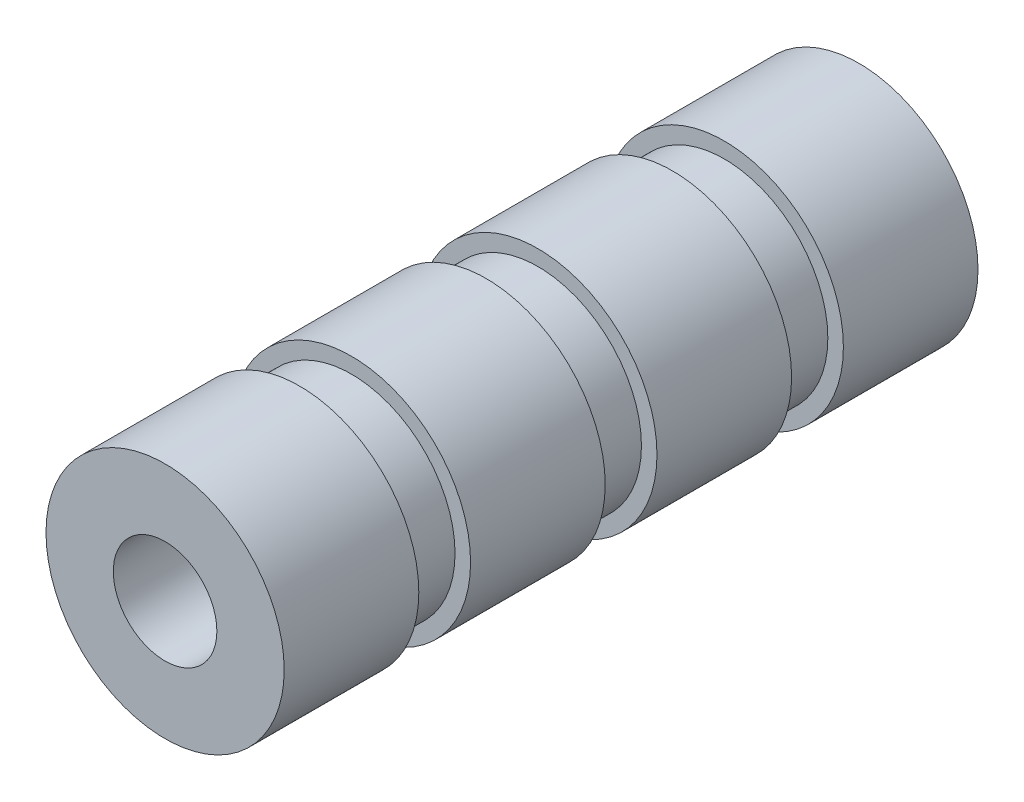
SolidWorks part; units mm, degrees
ref_plane "Front Plane" through (0, 0, 0) normal (0, 0, 1) x (1, 0, 0)
ref_plane "Top Plane" through (0, 0, 0) normal (0, 1, 0) x (1, 0, 0)
ref_plane "Right Plane" through (0, 0, 0) normal (1, 0, 0) x (0, 0, -1)
sketch "Sketch1" plane through (0, 0, 0) normal (0, 0, 1) x (1, 0, 0)
  circle A0 centre (0, 0) radius 11.5
  dimension "D1" = 23
extrude "Boss-Extrude1" add sketch "Sketch1" along normal blind 13
sketch "Sketch2" plane through (0, 0, 13) normal (0, 0, 1) x (1, 0, 0)
  circle A0 centre (0, 0) radius 10
  dimension "D1" = 20
extrude "Boss-Extrude2" add sketch "Sketch2" along normal blind 5
sketch "Sketch3" plane through (0, 0, 18) normal (0, 0, 1) x (1, 0, 0)
  circle A0 centre (0, 0) radius 11.5
extrude "Boss-Extrude3" add sketch "Sketch3" along normal blind 13
sketch "Sketch4" plane through (0, 0, 31) normal (0, 0, 1) x (1, 0, 0)
  circle A0 centre (0, 0) radius 10
extrude "Boss-Extrude4" add sketch "Sketch4" along normal blind 5
sketch "Sketch5" plane through (0, 0, 36) normal (0, 0, 1) x (1, 0, 0)
  circle A0 centre (0, 0) radius 11.5
extrude "Boss-Extrude5" add sketch "Sketch5" along normal blind 13
sketch "Sketch6" plane through (0, 0, 49) normal (0, 0, 1) x (1, 0, 0)
  circle A0 centre (0, 0) radius 10
extrude "Boss-Extrude6" add sketch "Sketch6" along normal blind 5
sketch "Sketch7" plane through (0, 0, 54) normal (0, 0, 1) x (1, 0, 0)
  circle A0 centre (0, 0) radius 11.5
extrude "Boss-Extrude7" add sketch "Sketch7" along normal blind 13
sketch "Sketch8" plane through (0, 0, 67) normal (0, 0, 1) x (1, 0, 0)
  circle A0 centre (0, 0) radius 5
extrude "Cut-Extrude1" cut sketch "Sketch8" against normal through all
